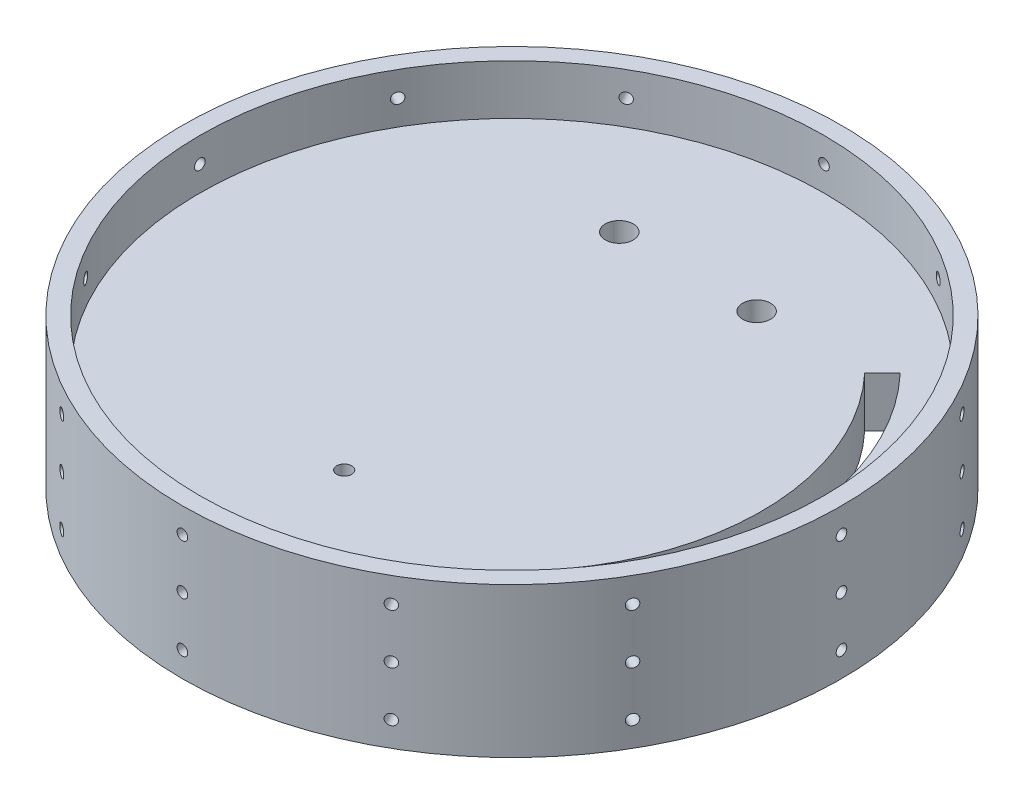
SolidWorks part; units mm, degrees
material "6061-T6 (SS)"
ref_plane "Front" through (0, 0, 0) normal (0, 0, 1) x (1, 0, 0)
ref_plane "Top" through (0, 0, 0) normal (0, 1, 0) x (1, 0, 0)
ref_plane "Right" through (0, 0, 0) normal (1, 0, 0) x (0, 0, -1)
sketch "Sketch1" plane through (0, 0, 0) normal (0, 1, 0) x (1, 0, 0)
  line L1 (0, 0) -> (127.635, 0)
  line L2 (0, 0) -> (0, 127.635)
  line L3 (0, 127.635) -> (127.635, 127.635)
  line L4 (127.635, 0) -> (127.635, 127.635)
  dimension "D1" = 127.635
  dimension "D2" = 127.635
extrude "Main Plate" add sketch "Sketch1" along normal blind 12.7
sketch "Sketch9" plane through (0, 12.7, 0) normal (0, 1, 0) x (1, 0, 0)
  circle A0 centre (63.8175, 63.8175) radius 85.725
  dimension "D1" = 171.45
extrude "Boss-Extrude1" add sketch "Sketch9" against normal up to surface (12.7 mm away) contours A0 up to face at (63.8175, 0, -63.8175)
sketch "Sketch10" plane through (0, 12.7, 0) normal (0, 1, 0) x (1, 0, 0)
  circle A0 centre (63.8175, 63.8175) radius 97.0396
  circle A1 centre (63.8175, 63.8175) radius 83.82
extrude "Cut-Extrude1" cut sketch "Sketch10" against normal blind 167.64 contours A0 | A1
sketch "Sketch11" plane through (0, 12.7, 0) normal (0, 1, 0) x (1, 0, 0)
  circle A0 centre (63.8175, 63.8175) radius 38.4175 construction
  circle A1 centre (63.8175, 63.8175) radius 42.8813 construction
  circle A2 centre (63.8175, 63.8175) radius 48.0528 construction
  circle A3 centre (63.8175, 63.8175) radius 83.82 construction
  dimension "D1" = 76.835
  dimension "D2" = 85.7626
  dimension "D3" = 96.1055
sketch "Sketch12" plane through (0, 12.7, 0) normal (0, 1, 0) x (1, 0, 0)
  line L0 (63.8175, 156.3529) -> (63.8175, -30.2474) construction
  line L1 (160.3603, 63.0527) -> (-31.9911, 63.0527) construction
  point P6 (63.8175, 63.0527)
sketch "Sketch2" plane through (0, 12.7, 0) normal (0, 1, 0) x (1, 0, 0)
  circle A0 centre (46.355, 108.585) radius 3.556
  circle A3 centre (63.8175, 63.8175) radius 48.0528 construction
  dimension "D1" = 7.112
extrude "U-Bolt Hole" cut sketch "Sketch2" against normal blind 12.7
pattern_linear "U-Bolt Pattern" count 2 spacing 34.925 along (1, 0, 0) of "U-Bolt Hole"
sketch "Sketch3" [suppressed] plane through (0, 12.7, 0) normal (0, 1, 0) x (1, 0, 0)
  circle A0 centre (25.4, 44.7675) radius 1.778
  circle A1 centre (63.8175, 63.8175) radius 42.8813 construction
  dimension "D1" = 3.556
extrude "Raptor Bolt Hole" [suppressed] cut sketch "Sketch3" against normal blind 12.7
pattern_linear "Raptor Bolt Pattern" [suppressed] count 2 spacing 38.1 along (0, 0, 1) count 2 spacing 76.835 along (-1, 0, 0)
sketch "Sketch4" [suppressed] plane through (0, 12.7, 0) normal (0, 1, 0) x (1, 0, 0)
  circle A0 centre (25.4, 63.8175) radius 12.7
  circle A1 centre (63.8175, 63.8175) radius 38.4175 construction
  dimension "D1" = 25.4
extrude "Co2 Cylinder Hole" [suppressed] cut sketch "Sketch4" against normal blind 12.7
pattern_linear "Co2 Pattern" [suppressed] count 2 spacing 76.835 along (-1, 0, 0)
sketch "Sketch13" plane through (0, 12.7, 0) normal (0, 1, 0) x (1, 0, 0)
  line L0 (63.8175, 156.3529) -> (63.8175, -30.2474) construction
  circle A0 centre (63.8175, 21.1558) radius 1.905
  dimension "D1" = 3.81
extrude "Cut-Extrude2" cut sketch "Sketch13" against normal up to surface (12.7 mm away) up to face at (81.28, 0, -105.029)
sketch "Sketch14" plane through (0, 12.7, 0) normal (0, 1, 0) x (1, 0, 0)
  line L0 (201.1692, 63.8175) -> (-73.4523, 63.8175) construction
ref_plane "Plane1" through (0, 0, -63.8175) normal (0, 0, -1) x (-1, 0, 0)
ref_plane "Plane3" through (0, 6.35, 0) normal (0, 1, 0) x (1, 0, 0)
sketch "Sketch16" plane through (0, 12.7, 0) normal (0, 1, 0) x (1, 0, 0)
  line L0 (63.8175, 63.8175) -> (123.0872, 123.0872) construction
  line L1 (63.8175, 63.8175) -> (123.0872, 4.5478) construction
  line L2 (87.3125, 63.8175) -> (-87.3125, 63.8175) construction
  line L3 (107.3987, 20.2363) -> (111.8888, 15.7462)
  line L4 (108.6773, 108.6773) -> (113.1913, 113.1913)
  circle A0 centre (63.8175, 63.8175) radius 83.82 construction
  arc A1 (113.1913, 113.1913) -> (111.8888, 15.7462) centre (62.4974, 65.1376) cw
  arc A2 (108.6773, 108.6773) -> (107.3987, 20.2363) centre (62.4754, 65.1156) cw
  dimension "D3" = 69.85
  dimension "D4" = 63.5
  dimension "D1" = 45
  dimension "D2" = 90
  dimension "D5" = 6.35
  dimension "D6" = 6.3837
extrude "Cut-Extrude4" cut sketch "Sketch16" against normal blind 15.24
ref_plane "Plane2" through (-20.0025, 0, 0) normal (-1, 0, 0) x (0, 0, 1)
sketch "Sketch18" plane through (0, 6.35, 0) normal (0, 1, 0) x (1, 0, 0)
  circle A0 centre (63.8175, 63.8175) radius 83.82
  circle A1 centre (63.8175, 63.8175) radius 79.375
  dimension "D1" = 158.75
extrude "Boss-Extrude2" add sketch "Sketch18" along normal mid plane 38.1
sketch "Sketch15" plane through (-20.0025, 0, 0) normal (-1, 0, 0) x (0, 0, 1)
  line L0 (-63.8175, 87.3125) -> (-63.8175, -87.3125) construction
  line L1 (20.0025, 12.7) -> (-147.6375, 12.7) construction
  line L2 (-147.6375, -12.7) -> (20.0025, -12.7) construction
  line L3 (15.5575, 25.4) -> (-143.1925, 25.4) construction
  circle A0 centre (-63.8175, 6.35) radius 1.3526
  circle A1 centre (-63.8175, 19.05) radius 1.3525
  circle A2 centre (-63.8175, -6.35) radius 1.3526
  dimension "D1" = 2.7051
  dimension "D2" = 6.35
  dimension "D3" = 2.7051
  dimension "D4" = 2.7051
  dimension "D5" = 6.35
  dimension "D6" = 6.35
extrude "Cut-Extrude3" cut sketch "Sketch15" against normal blind 15.24
pattern_circular "CirPattern1" count 12 over 360 about axis through (63.8175, 0, -63.8175) along (0, 1, 0) of "Cut-Extrude3"
